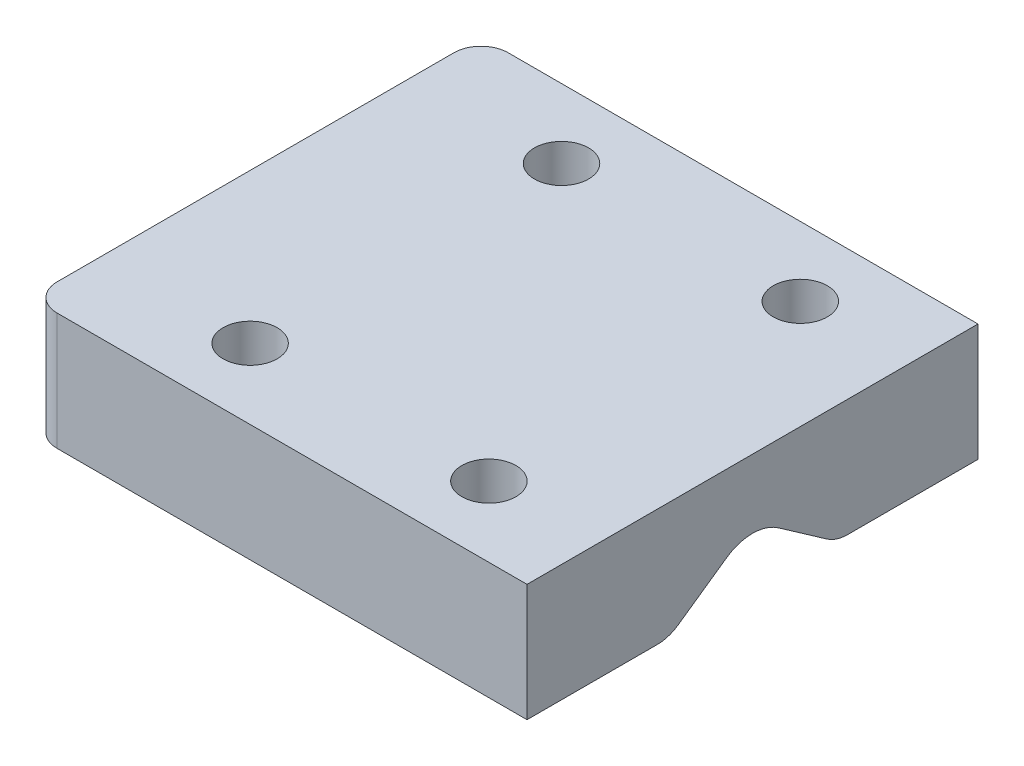
SolidWorks part; units mm, degrees
ref_plane "Front Plane" through (0, 0, 0) normal (0, 0, 1) x (1, 0, 0)
ref_plane "Top Plane" through (0, 0, 0) normal (0, 1, 0) x (1, 0, 0)
ref_plane "Right Plane" through (0, 0, 0) normal (1, 0, 0) x (0, 0, -1)
sketch "Sketch6" plane through (0, 68, 0) normal (0, 1, 0) x (1, 0, 0)
  line L1 (27.5, 25) -> (-27.5972, 25)
  line L2 (27.5, 25) -> (27.5, -25)
  line L3 (27.5, -25) -> (-27.5972, -25)
  line L4 (-27.5972, 25) -> (-27.5972, -25)
  line L5 (-24.5, -25) -> (27.5, -25) construction
extrude "Main Body" add sketch "Sketch6" along normal blind 13
sketch "Sketch7" plane through (27.5, 0, 0) normal (1, 0, 0) x (0, 0, -1)
  line L0 (0, 74.5) -> (-9.283, 68)
  line L1 (-25, 68) -> (25, 68) construction
  line L3 (0, 74.5) -> (9.283, 68)
  line L4 (9.283, 68) -> (0, 61.5)
  line L5 (0, 61.5) -> (-9.283, 68)
  line L6 (0, 74.5) -> (0, 61.5) construction
  dimension "D1" = 110
  dimension "D2" = 13
extrude "Main Hole" cut sketch "Sketch7" against normal through all
fillet "Exterior Fillet" radius 3 2 edges at (-27.5972, 74.5, -25) (-27.5972, 74.5, 25)
sketch "Sketch9" plane through (0, 81, 0) normal (0, 1, 0) x (1, 0, 0)
  circle A0 centre (15.4737, -17.2012) radius 3
  circle A1 centre (-11, -17.2012) radius 3
  circle A2 centre (15.4737, 17.3243) radius 3
  circle A3 centre (-11, 17.3243) radius 3
extrude "Bolt Holes" cut sketch "Sketch9" against normal through all
fillet "Top Hole Fillet" radius 5 1 edges at (-0.0486, 74.5, 0)
fillet "Side Hole Fillet" radius 4 2 edges at (-0.0486, 68, -9.283) (-0.0486, 68, 9.283)
